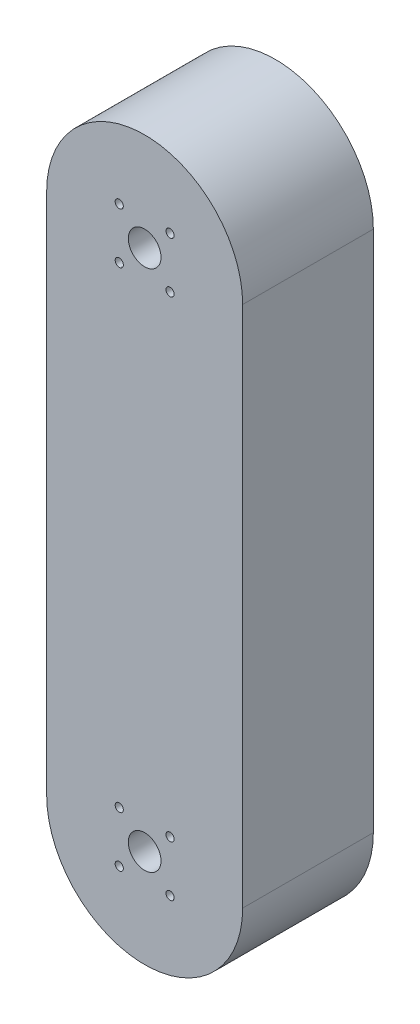
SolidWorks part; units mm, degrees
ref_plane "Front Plane" through (0, 0, 0) normal (0, 0, 1) x (1, 0, 0)
ref_plane "Top Plane" through (0, 0, 0) normal (0, 1, 0) x (1, 0, 0)
ref_plane "Right Plane" through (0, 0, 0) normal (1, 0, 0) x (0, 0, -1)
sketch "Sketch1" plane through (0, 0, 0) normal (0, 0, 1) x (1, 0, 0)
  line L2 (19.05, 50.8) -> (19.05, -50.8)
  line L4 (-19.05, 50.8) -> (-19.05, -50.8)
  line L5 (19.05, 50.8) -> (-19.05, -50.8) construction
  line L6 (19.05, -50.8) -> (-19.05, 50.8) construction
  arc A0 (-19.05, 50.8) -> (19.05, 50.8) centre (0, 50.8) cw
  arc A1 (-19.05, -50.8) -> (19.05, -50.8) centre (0, -50.8) ccw
  point P0 (0, 0)
  dimension "D1" = 101.6
  dimension "D2" = 38.1
extrude "Boss-Extrude1" add sketch "Sketch1" along normal blind 25.4
sketch "Sketch2" plane through (0, 0, 25.4) normal (0, 0, 1) x (1, 0, 0)
  line L0 (-4.9391, 55.7391) -> (4.9391, 45.8609) construction
  line L1 (4.9391, 55.7391) -> (-4.9391, 45.8609) construction
  line L2 (0, 50.8) -> (0, 59.0413) construction
  circle A0 centre (0, 50.8) radius 3.175
  circle A1 centre (-4.9391, 55.7391) radius 0.7938
  circle A2 centre (-4.9391, 45.8609) radius 0.7937
  circle A3 centre (4.9391, 55.7391) radius 0.7938
  circle A4 centre (4.9391, 45.8609) radius 0.7938
  point P8 (0, 50.8)
  point P9 (0, 50.8)
  dimension "D1" = 6.35
  dimension "D4" = 1.5875
  dimension "D2" = 45
  dimension "D3" = 13.97
extrude "Cut-Extrude1" cut sketch "Sketch2" against normal up to next (25.4 mm away)
mirror "Mirror1" about plane through (0, 0, 0) normal (0, 1, 0) of "Cut-Extrude1"
